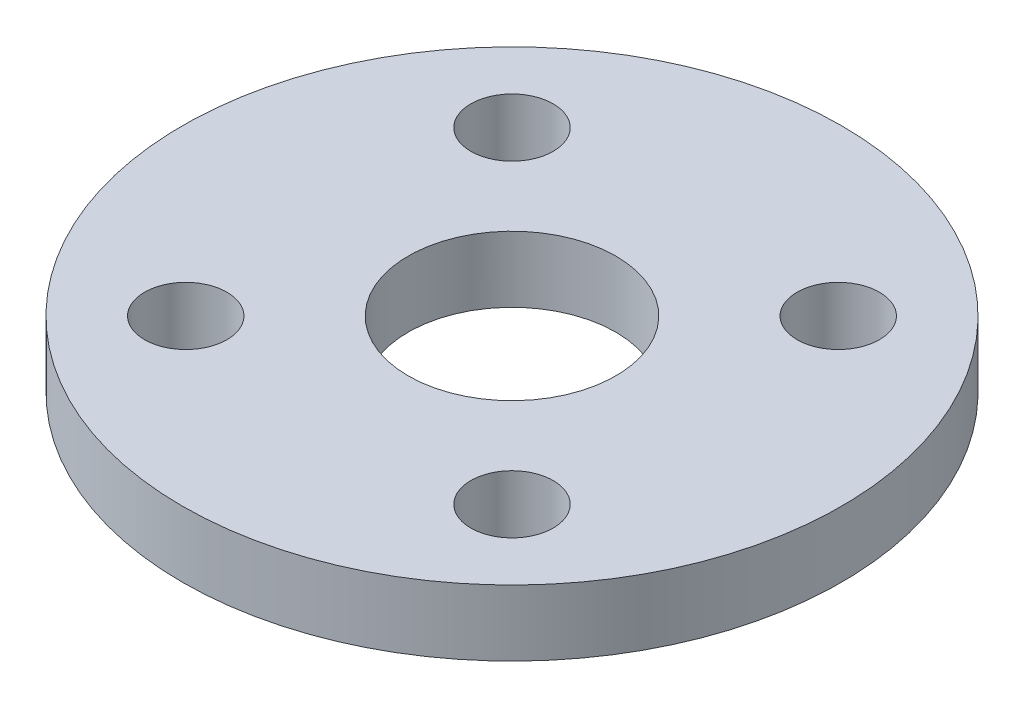
SolidWorks part; units mm, degrees
ref_plane "Спереди" through (0, 0, 0) normal (0, 0, 1) x (1, 0, 0)
ref_plane "Сверху" through (0, 0, 0) normal (0, 1, 0) x (1, 0, 0)
ref_plane "Справа" through (0, 0, 0) normal (1, 0, 0) x (0, 0, -1)
sketch "Эскиз1" plane through (0, 0, 0) normal (0, 0, 1) x (1, 0, 0)
  line L0 (10, 2) -> (0, 2)
  line L1 (0, 2) -> (0, 0)
  line L2 (0, 0) -> (10, 0)
  line L3 (10, 0) -> (10, 2)
  line L4 (0, 2) -> (0, 0) construction
revolve "Повернуть1" add sketch "Эскиз1" angle 360 about L4
sketch "Эскиз2" plane through (0, 2, 0) normal (0, 1, 0) x (-1, 0, 0)
  circle A0 centre (0, 0) radius 4.5
extrude "Бобышка-Вытянуть1" add sketch "Эскиз2" along normal blind 2.5
sketch "Эскиз3" plane through (0, 4.5, 0) normal (0, 1, 0) x (-1, 0, 0)
  line L0 (-2.7115, 1.0284) -> (-2.4779, 0.6107)
  line L1 (-2.4779, 0.6107) -> (-2.8789, 0.3496)
  line L2 (-2.8789, 0.3496) -> (-2.552, 0)
  line L3 (-2.552, 0) -> (-2.8789, -0.3496)
  line L4 (-2.8789, -0.3496) -> (-2.4779, -0.6107)
  line L5 (-2.4779, -0.6107) -> (-2.7115, -1.0284)
  line L6 (-2.7115, -1.0284) -> (-2.2597, -1.186)
  line L7 (-2.2597, -1.186) -> (-2.3867, -1.6474)
  line L8 (-2.3867, -1.6474) -> (-1.9102, -1.6923)
  line L9 (-1.9102, -1.6923) -> (-1.9231, -2.1707)
  line L10 (-1.9231, -2.1707) -> (-1.4497, -2.1003)
  line L11 (-1.4497, -2.1003) -> (-1.3477, -2.5678)
  line L12 (-1.3477, -2.5678) -> (-0.905, -2.3862)
  line L13 (-0.905, -2.3862) -> (-0.694, -2.8157)
  line L14 (-0.694, -2.8157) -> (-0.3076, -2.5334)
  line L15 (-0.3076, -2.5334) -> (0, -2.9)
  line L16 (0, -2.9) -> (0.3076, -2.5334)
  line L17 (0.3076, -2.5334) -> (0.694, -2.8157)
  line L18 (0.694, -2.8157) -> (0.905, -2.3862)
  line L19 (0.905, -2.3862) -> (1.3477, -2.5678)
  line L20 (1.3477, -2.5678) -> (1.4497, -2.1003)
  line L21 (1.4497, -2.1003) -> (1.9231, -2.1707)
  line L22 (1.9231, -2.1707) -> (1.9102, -1.6923)
  line L23 (1.9102, -1.6923) -> (2.3867, -1.6474)
  line L24 (2.3867, -1.6474) -> (2.2597, -1.186)
  line L25 (2.2597, -1.186) -> (2.7115, -1.0284)
  line L26 (2.7115, -1.0284) -> (2.4779, -0.6107)
  line L27 (2.4779, -0.6107) -> (2.8789, -0.3496)
  line L28 (2.8789, -0.3496) -> (2.552, 0)
  line L29 (2.552, 0) -> (2.8789, 0.3496)
  line L30 (2.8789, 0.3496) -> (2.4779, 0.6107)
  line L31 (2.4779, 0.6107) -> (2.7115, 1.0284)
  line L32 (2.7115, 1.0284) -> (2.2597, 1.186)
  line L33 (2.2597, 1.186) -> (2.3867, 1.6474)
  line L34 (2.3867, 1.6474) -> (1.9102, 1.6923)
  line L35 (1.9102, 1.6923) -> (1.9231, 2.1707)
  line L36 (1.9231, 2.1707) -> (1.4497, 2.1003)
  line L37 (1.4497, 2.1003) -> (1.3477, 2.5678)
  line L38 (1.3477, 2.5678) -> (0.905, 2.3862)
  line L39 (0.905, 2.3862) -> (0.694, 2.8157)
  line L40 (0.694, 2.8157) -> (0.3076, 2.5334)
  line L41 (0.3076, 2.5334) -> (0, 2.9)
  line L42 (0, 2.9) -> (-0.3076, 2.5334)
  line L43 (-0.3076, 2.5334) -> (-0.694, 2.8157)
  line L44 (-0.694, 2.8157) -> (-0.905, 2.3862)
  line L45 (-0.905, 2.3862) -> (-1.3477, 2.5678)
  line L46 (-1.3477, 2.5678) -> (-1.4497, 2.1003)
  line L47 (-1.4497, 2.1003) -> (-1.9231, 2.1707)
  line L48 (-1.9231, 2.1707) -> (-1.9102, 1.6923)
  line L49 (-1.9102, 1.6923) -> (-2.3867, 1.6474)
  line L50 (-2.3867, 1.6474) -> (-2.2597, 1.186)
  line L51 (-2.2597, 1.186) -> (-2.7115, 1.0284)
extrude "Вырез-Вытянуть1" cut sketch "Эскиз3" against normal blind 3.6
hole_wizard "Диаметр отверстия Ø3.0 (3)1" positions "Эскиз5" profile "Эскиз4" hole size "Ø3.0" standard "Ansi Metric"
sketch "Эскиз5" plane through (0, 0.9, 0) normal (0, 1, 0) x (1, 0, 0)
  point P0 (0, 0)
sketch "Эскиз4" plane through (0, 0.9, 0) normal (1, 0, 0) x (0, 0, 1)
  line L0 (0, 0) -> (0, 0.9)
  line L1 (0, 0.9) -> (1.5, 0.9)
  line L2 (1.5, 0.9) -> (1.5, 0)
  line L5 (1.5, 0) -> (0, 0)
  line L11 (0, -6.35) -> (0, 107.95) construction
  dimension "Диаметр сквозного отверстия" = 3
  dimension "Глубина сквозного отверстия" = 0.9
hole_wizard "Диаметр отверстия Ø2.5 (2.5)1" positions "Эскиз7" profile "Эскиз6" hole size "Ø2.5" standard "Ansi Metric"
sketch "Эскиз7" plane through (0, 2, 0) normal (0, 1, 0) x (1, 0, 0)
  point P0 (-4.9497, 4.9497)
  point P1 (4.9497, 4.9497)
  point P2 (4.9497, -4.9497)
  point P3 (-4.9497, -4.9497)
sketch "Эскиз6" plane through (-4.9497, 2, -4.9497) normal (1, 0, 0) x (0, 0, 1)
  line L0 (0, 0) -> (0, 2)
  line L1 (0, 2) -> (1.25, 2)
  line L2 (1.25, 2) -> (1.25, 0)
  line L5 (1.25, 0) -> (0, 0)
  line L11 (0, -6.35) -> (0, 107.95) construction
  dimension "Диаметр сквозного отверстия" = 2.5
  dimension "Глубина сквозного отверстия" = 2
chamfer "Фаска1" distance 0.1406 angle 43.077 26 edges at (-2.4779, 2.7, -0.6107) (-2.4779, 2.7, 0.6107) (-2.2597, 2.7, -1.186) (-2.2597, 2.7, 1.186) (2.552, 2.7, 0) (-1.9102, 2.7, -1.6923) (-1.9102, 2.7, 1.6923) (-1.4497, 2.7, -2.1003) (-1.4497, 2.7, 2.1003) (-0.905, 2.7, -2.3862) (-0.905, 2.7, 2.3862) (2.4779, 2.7, 0.6107) (-0.3076, 2.7, -2.5334) (0.3076, 2.7, -2.5334) (-0.3076, 2.7, 2.5334) (0.3076, 2.7, 2.5334) (0.905, 2.7, -2.3862) (0.905, 2.7, 2.3862) (1.4497, 2.7, -2.1003) (1.4497, 2.7, 2.1003) (1.9102, 2.7, -1.6923) (1.9102, 2.7, 1.6923) (2.2597, 2.7, -1.186) (2.2597, 2.7, 1.186) (2.4779, 2.7, -0.6107) (-2.552, 2.7, 0)
sketch "Эскиз8" plane through (0, 4.5, 0) normal (0, 1, 0) x (1, 0, 0)
  circle A0 centre (0, 0) radius 4.5 construction
  circle A1 centre (0, 0) radius 4.5
extrude "Вырез-Вытянуть2" cut sketch "Эскиз8" against normal up to surface (4.5 mm away) up to face at (-4.9497, 0, -3.6997)
sketch "Эскиз9" plane through (0, 0, 0) normal (0, -1, 0) x (1, 0, 0)
  circle A0 centre (0, 0) radius 4.5 construction
  circle A1 centre (0, 0) radius 4.5
  circle A2 centre (0, 0) radius 3.15
  dimension "D1" = 6.3
extrude "Бобышка-Вытянуть2" add sketch "Эскиз9" against normal up to surface (2 mm away) up to face at (-4.9497, 2, -3.6997)
